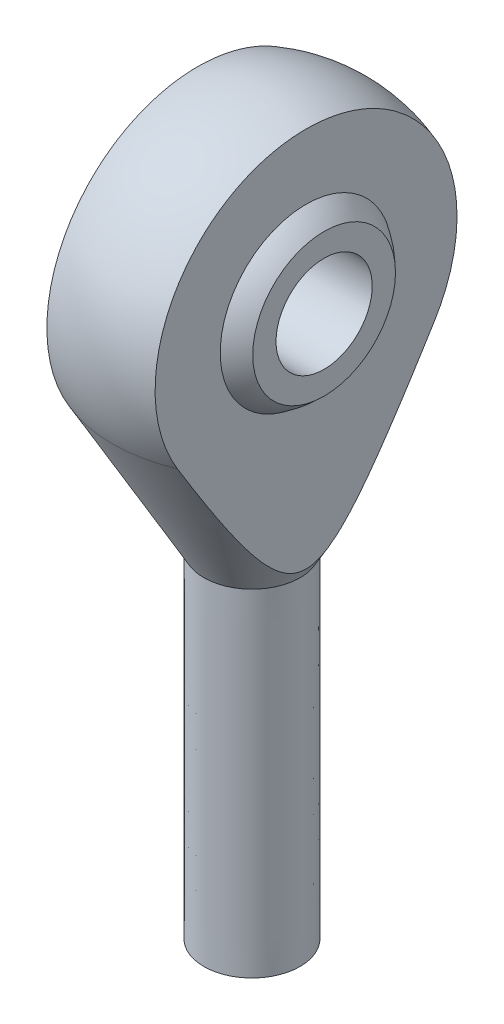
SolidWorks part; units mm, degrees
ref_plane "Płaszczyzna XY" through (0, 0, 0) normal (0, 0, 1) x (1, 0, 0)
ref_plane "Płaszczyzna XZ" through (0, 0, 0) normal (0, 1, 0) x (1, 0, 0)
ref_plane "Płaszczyzna YZ" through (0, 0, 0) normal (1, 0, 0) x (0, 0, -1)
sketch "Szkic1" plane through (0, 0, 0) normal (0, 0, 1) x (1, 0, 0)
  line L0 (-3, 0) -> (3, 0)
  line L1 (3, 0) -> (3, 21)
  line L2 (3, 21) -> (-3, 21) construction
  line L3 (-3, 21) -> (-3, 0)
  line L4 (-3, 21) -> (-8.6992, 31.0772)
  line L5 (3, 21) -> (8.7057, 31.0704)
  line L6 (0.0052, 46) -> (0, 0)
  arc A0 (8.7057, 31.0704) -> (-8.6992, 31.0772) centre (0.0052, 36) ccw
  point P4 (0, 0)
  dimension "D2" = 20
  dimension "D1" = 6
  dimension "D3" = 36
  dimension "GL" = 21
revolve "Obrót4" add sketch "Szkic1" angle 360 about L6
sketch "Szkic2" plane through (0, 0, 0) normal (0, 0, 1) x (1, 0, 0)
  line L0 (-20, 46) -> (20, 46)
  line L1 (20, 46) -> (20, 10.8573)
  line L2 (20, 10.8573) -> (3.375, 21.6537)
  line L3 (3.375, 21.6537) -> (3.375, 46)
  line L4 (-20, 46) -> (-20, 10.8667)
  line L5 (-20, 10.8667) -> (-3.375, 21.6631)
  line L6 (-3.375, 21.6631) -> (-3.375, 46)
  line L7 (0, 35.7786) -> (0, -51.7786) construction
  line L8 (-8.6992, 31.0772) -> (-3, 21) construction
  line L9 (3.0047, 20.9993) -> (8.7062, 31.0753) construction
  point P9 (0, 46)
  point P12 (0, -8)
  dimension "M" = 6.75
  dimension "D1" = 3.375
  dimension "D2" = 40
  dimension "D3" = 54
  dimension "D4" = 123
  dimension "D5" = 123
extrude "Wytnij-wyciągnięcie1" cut sketch "Szkic2" against normal through all both and the other way through all contours L5 L6 L0 L4 | L3 L2 L1 L0
sketch "Szkic3" plane through (0, 0, 0) normal (1, 0, 0) x (0, 0, -1)
  line L3 (0, 0) -> (0, 10.5388) construction
ref_plane "Płaszczyzna1" through (0, 0, 0) normal (0, 0, -1) x (0, 1, 0)
sketch "Szkic4" plane through (0, 0, 0) normal (0, 0, -1) x (0, 1, 0)
  line L0 (-200000, 0) -> (200010.5388, 0) construction
  line L1 (35.9993, -1) -> (35.9993, 16.5523) construction
  line L2 (31.5493, -4.5) -> (40.4493, -4.5)
  line L3 (31.5493, -4.5) -> (31.5493, 4.5)
  line L4 (31.5493, 4.5) -> (40.4493, 4.5)
  line L5 (40.4493, -4.5) -> (40.4493, 4.5)
  line L6 (31.5493, -4.5) -> (40.4493, 4.5) construction
  line L7 (31.5493, 4.5) -> (40.4493, -4.5) construction
  line L8 (32.9993, -4.5) -> (38.9993, -4.5)
  line L9 (32.9993, -4.5) -> (32.9993, 4.5)
  line L10 (32.9993, 4.5) -> (38.9993, 4.5)
  line L11 (38.9993, -4.5) -> (38.9993, 4.5)
  line L12 (32.9993, -4.5) -> (38.9993, 4.5) construction
  line L13 (32.9993, 4.5) -> (38.9993, -4.5) construction
  circle A0 centre (35.9993, 0) radius 6.3287
  dimension "D1" = 6
  dimension "D2" = 8.9
  dimension "D3" = 9
  dimension "D4" = 36
revolve "Obrót5" add sketch "Szkic4" angle 360 about L1
sketch "Szkic8" plane through (0, 0, 0) normal (1, 0, 0) x (0, 0, -1)
  circle A0 centre (0, 35.9993) radius 3
extrude "Wytnij-wyciągnięcie3" cut sketch "Szkic8" against normal through all both and the other way through all
sketch "Szkic9" [suppressed] plane through (0, 0, 0) normal (1, 0, 0) x (0, 0, -1)
  circle A0 centre (0, 41.9991) radius 4
extrude "Wytnij-wyciągnięcie4" [suppressed] cut sketch "Szkic9" against normal through all both and the other way through all
ref_point "Point1" [suppressed]
equation "\"D2@Szkic2\"=2*\"D2@Szkic1\""
equation "\"D1@Szkic2\"=\"M@Szkic2\"/2mm"
